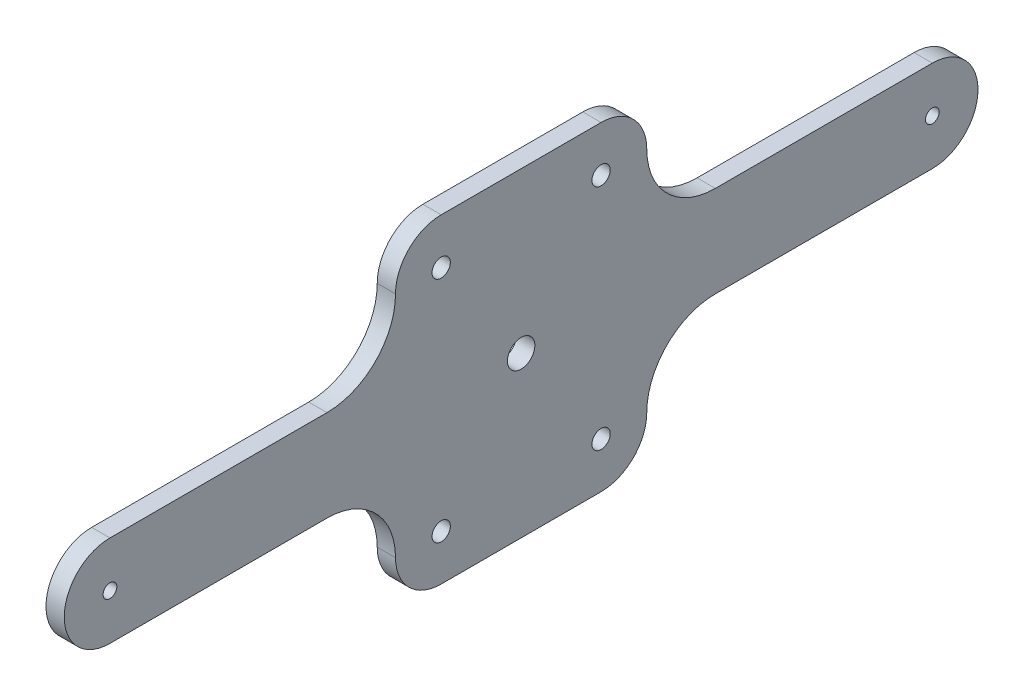
SolidWorks part; units mm, degrees
material "Acrylic (Medium-high impact)"
ref_plane "Front Plane" through (0, 0, 0) normal (0, 0, 1) x (1, 0, 0)
ref_plane "Top Plane" through (0, 0, 0) normal (0, 1, 0) x (1, 0, 0)
ref_plane "Right Plane" through (0, 0, 0) normal (1, 0, 0) x (0, 0, -1)
sketch "Sketch1" plane through (0, 0, 0) normal (1, 0, 0) x (0, 0, -1)
  line L0 (0, 0) -> (-114.2997, 0) construction
  line L1 (105, -37.5) -> (-105, -37.5)
  line L2 (105, -37.5) -> (105, 37.5)
  line L3 (105, 37.5) -> (-105, 37.5)
  line L4 (-105, -37.5) -> (-105, 37.5)
  line L5 (105, -37.5) -> (-105, 37.5) construction
  line L6 (105, 37.5) -> (-105, -37.5) construction
  point P0 (0, 0)
  dimension "D1" = 210
  dimension "D2" = 75
extrude "Boss-Extrude1" add sketch "Sketch1" along normal blind 4
sketch "Sketch2" plane through (4, 0, 0) normal (1, 0, 0) x (0, 0, -1)
  circle A2 centre (-90, 0) radius 1.5
  dimension "D1" = 3
  dimension "D2" = 90
extrude "Cut-Extrude1" cut sketch "Sketch2" against normal through all
sketch "Sketch3" plane through (4, 0, 0) normal (1, 0, 0) x (0, 0, -1)
  line L0 (0, 55) -> (0, -55) construction
  line L1 (55, 0) -> (-55, 0) construction
  circle A0 centre (-17.5, 25) radius 2
  dimension "D1" = 4
  dimension "D2" = 17.5
  dimension "D3" = 25
extrude "Cut-Extrude2" cut sketch "Sketch3" against normal through all
sketch "Sketch4" plane through (4, 0, 0) normal (1, 0, 0) x (0, 0, -1)
  line L2 (-105, 0) -> (-105, 37.5)
  line L16 (-90, 10) -> (-42.5, 10)
  line L17 (-100, 0) -> (-105, 0)
  line L18 (-17.5, 35) -> (0, 35)
  line L19 (0, 35) -> (0, 37.5)
  line L20 (105, 37.5) -> (-105, 37.5) construction
  line L21 (0, 37.5) -> (-105, 37.5)
  circle A19 centre (-90, 0) radius 1.5 construction
  arc A30 (-90, 10) -> (-100, 0) centre (-90, 0) ccw
  arc A33 (-17.5, 35) -> (-27.5, 25) centre (-17.5, 25) ccw
  arc A36 (-42.5, 10) -> (-27.5, 25) centre (-42.5, 25) ccw
  dimension "D1" = 10
  dimension "D2" = 20
  dimension "D4" = 0
extrude "Cut-Extrude3" cut sketch "Sketch4" against normal through all
mirror "Mirror2" about plane through (0, 0, 0) normal (0, 1, 0) of "Cut-Extrude3", "Cut-Extrude2"
mirror "Mirror3" about plane through (0, 0, 0) normal (0, 0, 1) of "Mirror2", "Cut-Extrude3", "Cut-Extrude1", "Cut-Extrude2"
sketch "Sketch5" plane through (4, 0, 0) normal (1, 0, 0) x (0, 0, -1)
  circle A0 centre (0, 0) radius 3
  dimension "D1" = 6
extrude "Cut-Extrude4" cut sketch "Sketch5" against normal through all
